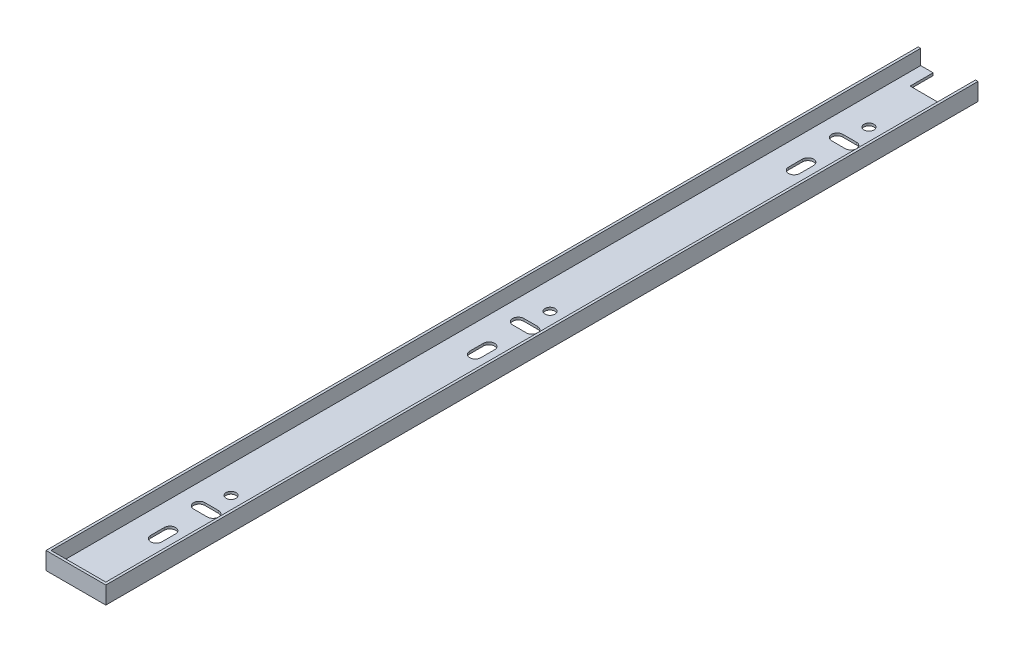
SolidWorks part; units mm, degrees
ref_plane "前视基准面" through (0, 0, 0) normal (0, 0, 1) x (1, 0, 0)
ref_plane "上视基准面" through (0, 0, 0) normal (0, 1, 0) x (1, 0, 0)
ref_plane "右视基准面" through (0, 0, 0) normal (1, 0, 0) x (0, 0, -1)
sketch "草图1" plane through (0, 0, 0) normal (0, 0, 1) x (1, 0, 0)
  line L0 (0, 11.8231) -> (0, -11.7592) construction
  line L1 (-12, 3.5) -> (-11, 3.5)
  line L2 (-12, 3.5) -> (-12, -3.5)
  line L3 (-12, -3.5) -> (12, -3.5)
  line L4 (12, 3.5) -> (12, -3.5)
  line L5 (-28.8801, 0) -> (21.8707, 0) construction
  line L6 (11, 3.5) -> (12, 3.5)
  line L8 (-11, 3.5) -> (-11, -2.5)
  line L9 (-11, -2.5) -> (11, -2.5)
  line L10 (11, 3.5) -> (11, -2.5)
  dimension "D1" = 7
  dimension "D2" = 24
  dimension "D3" = 1
  dimension "D4" = 1
extrude "凸台-拉伸1" add sketch "草图1" along normal blind 350
sketch "草图2" plane through (0, -3.5, 0) normal (0, -1, 0) x (1, 0, 0)
  line L0 (0, 374.0123) -> (0, -35.6413) construction
  line L1 (-2.75, 300) -> (2.75, 300)
  line L2 (2.75, 295.5) -> (-2.75, 295.5)
  line L3 (-12, 350) -> (12, 350) construction
  line L4 (-58.0288, 297.75) -> (53.1855, 297.75) construction
  line L5 (-2.25, 317.75) -> (-2.25, 312.25)
  line L6 (2.25, 317.75) -> (2.25, 312.25)
  line L7 (-2.25, 189.75) -> (-2.25, 184.25)
  line L8 (-58.0288, 169.75) -> (53.1855, 169.75) construction
  line L9 (2.75, 167.5) -> (-2.75, 167.5)
  line L10 (-2.75, 172) -> (2.75, 172)
  line L11 (2.25, 189.75) -> (2.25, 184.25)
  line L12 (-2.25, 61.75) -> (-2.25, 56.25)
  line L13 (-58.0288, 41.75) -> (53.1855, 41.75) construction
  line L14 (2.75, 39.5) -> (-2.75, 39.5)
  line L15 (-2.75, 44) -> (2.75, 44)
  line L16 (2.25, 61.75) -> (2.25, 56.25)
  line L17 (-12, 0) -> (12, 0) construction
  line L18 (-6, 9.2398) -> (6, 9.2398)
  line L19 (-6, 9.2398) -> (-6, 0)
  line L20 (-6, 0) -> (6, 0)
  line L21 (6, 9.2398) -> (6, 0)
  arc A0 (-2.75, 300) -> (-2.75, 295.5) centre (-2.75, 297.75) ccw
  arc A1 (2.75, 300) -> (2.75, 295.5) centre (2.75, 297.75) cw
  circle A2 centre (0, 287.75) radius 2
  arc A3 (2.25, 317.75) -> (-2.25, 317.75) centre (0, 317.75) ccw
  arc A4 (-2.25, 312.25) -> (2.25, 312.25) centre (0, 312.25) ccw
  arc A5 (2.25, 189.75) -> (-2.25, 189.75) centre (0, 189.75) ccw
  arc A6 (2.75, 172) -> (2.75, 167.5) centre (2.75, 169.75) cw
  arc A7 (-2.25, 184.25) -> (2.25, 184.25) centre (0, 184.25) ccw
  circle A8 centre (0, 159.75) radius 2
  arc A9 (-2.75, 172) -> (-2.75, 167.5) centre (-2.75, 169.75) ccw
  arc A10 (2.25, 61.75) -> (-2.25, 61.75) centre (0, 61.75) ccw
  arc A11 (2.75, 44) -> (2.75, 39.5) centre (2.75, 41.75) cw
  arc A12 (-2.25, 56.25) -> (2.25, 56.25) centre (0, 56.25) ccw
  circle A13 centre (0, 31.75) radius 2
  arc A14 (-2.75, 44) -> (-2.75, 39.5) centre (-2.75, 41.75) ccw
  dimension "D3" = 5.5
  dimension "D4" = 4
  dimension "D5" = 2.25
  dimension "D8" = 10
  dimension "D11" = 4
  dimension "D12" = 128
  dimension "D17" = 4
  dimension "D18" = 128
  dimension "D1" = 4.5
  dimension "D2" = 50
  dimension "D6" = 5.5
  dimension "D7" = 32.25
  dimension "D9" = 4.5
  dimension "D10" = 5.5
  dimension "D13" = 5.5
  dimension "D14" = 10
  dimension "D15" = 4.5
  dimension "D16" = 5.5
  dimension "D19" = 5.5
  dimension "D20" = 10
  dimension "D21" = 14.5
  dimension "D22" = 14.5
  dimension "D23" = 12
extrude "切除-拉伸1" cut sketch "草图2" against normal blind 3500
sketch "草图3" plane through (0, -2.5, 0) normal (0, 1, 0) x (1, 0, 0)
  line L0 (-11, -350) -> (-11, 0) construction
  line L1 (-11, -349) -> (11, -349)
  line L2 (-11, -349) -> (-11, -350)
  line L3 (-11, -350) -> (11, -350)
  line L4 (11, -349) -> (11, -350)
  dimension "D1" = 1
extrude "凸台-拉伸2" add sketch "草图3" along normal blind 6
